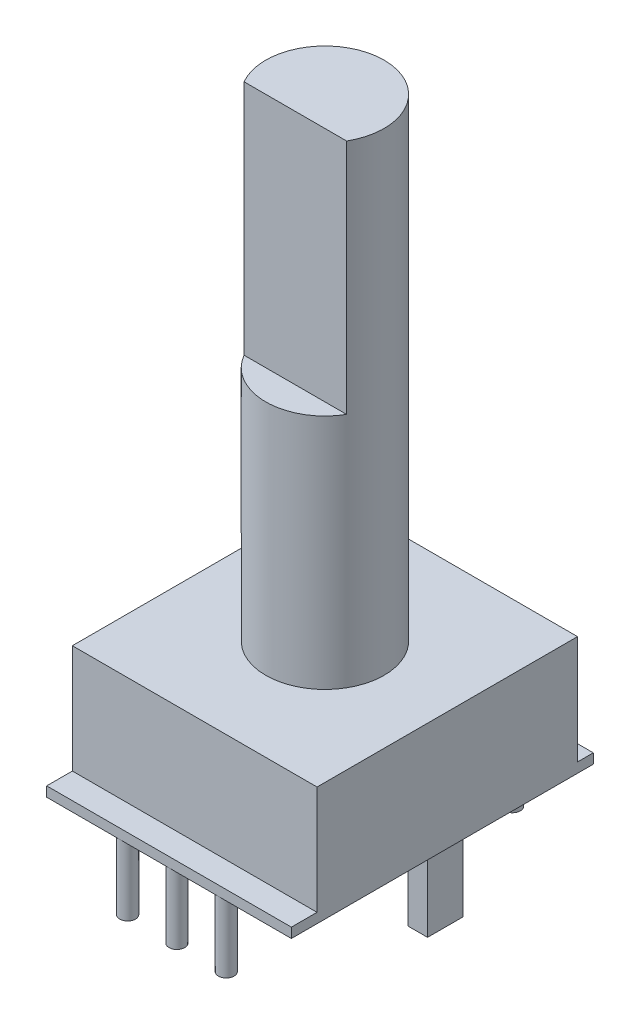
SolidWorks part; units mm, degrees
ref_plane "Front Plane" through (0, 0, 0) normal (0, 0, 1) x (1, 0, 0)
ref_plane "Top Plane" through (0, 0, 0) normal (0, 1, 0) x (1, 0, 0)
ref_plane "Right Plane" through (0, 0, 0) normal (1, 0, 0) x (0, 0, -1)
sketch "Sketch1" plane through (0, 0, 0) normal (0, 1, 0) x (1, 0, 0)
  line L1 (-6.1, 0.9) -> (-5.1, 0.9)
  line L2 (-6.1, 0.9) -> (-6.1, -0.9)
  line L3 (-6.1, -0.9) -> (-5.1, -0.9)
  line L4 (-5.1, 0.9) -> (-5.1, -0.9)
  line L5 (5.1, 0.9) -> (6.1, 0.9)
  line L6 (5.1, 0.9) -> (5.1, -0.9)
  line L7 (5.1, -0.9) -> (6.1, -0.9)
  line L8 (6.1, 0.9) -> (6.1, -0.9)
  circle A0 centre (-2.5, -7.5) radius 0.4
  circle A1 centre (0, -7.5) radius 0.4
  circle A2 centre (2.5, -7.5) radius 0.4
  circle A3 centre (2.5, 7) radius 0.4
  circle A4 centre (-2.5, 7) radius 0.4
  point P18 (-5.1, 0)
  point P20 (0, 0)
  point P21 (0, 0)
  point P22 (0, 0)
  point P23 (0, 0)
  point P24 (0, 0)
  point P25 (-5.6, 0.9)
  point P26 (5.6, 0.9)
  dimension "D7" = 0.8
  dimension "D1" = 5
  dimension "D2" = 2.5
  dimension "D3" = 11.2
  dimension "D4" = 5.6
  dimension "D5" = 1
  dimension "D6" = 1.8
  dimension "D8" = 7
  dimension "D9" = 7.5
extrude "Boss-Extrude1" add sketch "Sketch1" against normal blind 3.5
sketch "Sketch2" plane through (0, 0, 0) normal (0, 1, 0) x (1, 0, 0)
  line L1 (-6.2, 6.6) -> (6.2, 6.6)
  line L2 (-6.2, 6.6) -> (-6.2, -6.6)
  line L3 (-6.2, -6.6) -> (6.2, -6.6)
  line L4 (6.2, 6.6) -> (6.2, -6.6)
  line L5 (-6.2, 6.6) -> (6.2, -6.6) construction
  line L6 (-6.2, -6.6) -> (6.2, 6.6) construction
  point P0 (0, 0)
  dimension "D1" = 13.2
  dimension "D2" = 12.4
extrude "Boss-Extrude2" add sketch "Sketch2" along normal blind 6
sketch "Sketch3" plane through (0, 0, 0) normal (0, 1, 0) x (1, 0, 0)
  line L0 (6.2, -6.6) -> (6.2, 6.6) construction
  line L5 (-6.2, 7.4) -> (6.2, 7.4)
  line L6 (-6.2, 7.4) -> (-6.2, -7.9)
  line L7 (-6.2, -7.9) -> (6.2, -7.9)
  line L8 (6.2, 7.4) -> (6.2, -7.9)
  line L9 (-6.2, 6.6) -> (-6.2, -6.6) construction
  circle A0 centre (-2.5, -7.5) radius 0.4 construction
  circle A1 centre (-2.5, 7) radius 0.4 construction
  point P0 (0, 0)
extrude "Boss-Extrude3" add sketch "Sketch3" along normal blind 0.5
sketch "Sketch4" plane through (0, 6, 0) normal (0, 1, 0) x (1, 0, 0)
  circle A0 centre (0, 0) radius 3
  dimension "D1" = 6
extrude "Boss-Extrude4" add sketch "Sketch4" along normal blind 24
sketch "Sketch5" plane through (0, 30, 0) normal (0, 1, 0) x (1, 0, 0)
  line L0 (-2.5981, -1.5) -> (2.5981, -1.5)
  line L1 (0, 0) -> (0, -3) construction
  line L2 (0, 0) -> (0, 3) construction
  arc A0 (-2.5981, -1.5) -> (2.5981, -1.5) centre (0, 0) ccw
  circle A1 centre (0, 0) radius 3 construction
  dimension "D1" = 4.5
extrude "Cut-Extrude1" cut sketch "Sketch5" against normal blind 12
equation "\"D2@Sketch1\"=\"D1@Sketch1\"/2"
equation "\"D4@Sketch1\"=\"D3@Sketch1\"/2"
